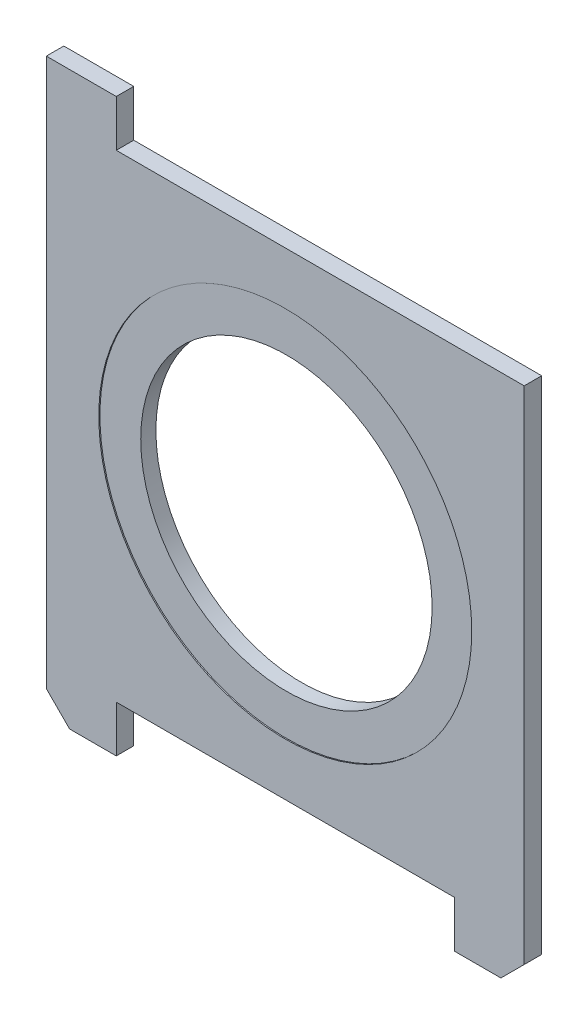
SolidWorks part; units mm, degrees
ref_plane "Plan de face" through (0, 0, 0) normal (0, 0, 1) x (1, 0, 0)
ref_plane "Plan de dessus" through (0, 0, 0) normal (0, 1, 0) x (1, 0, 0)
ref_plane "Plan de droite" through (0, 0, 0) normal (1, 0, 0) x (0, 0, -1)
sketch "Esquisse1" plane through (0, 0, 0) normal (0, 0, 1) x (1, 0, 0)
  line L1 (-20.5, -20.5) -> (20.5, -20.5)
  line L2 (-20.5, -20.5) -> (-20.5, 20.5)
  line L3 (-20.5, 20.5) -> (20.5, 20.5)
  line L4 (20.5, -20.5) -> (20.5, 20.5)
  line L5 (-20.5, -20.5) -> (20.5, 20.5) construction
  line L6 (-20.5, 20.5) -> (20.5, -20.5) construction
  point P0 (0, 0)
  dimension "D1" = 41
  dimension "D2" = 41
extrude "Boss.-Extru.1" add sketch "Esquisse1" along normal blind 1.5
sketch "Esquisse2" plane through (0, 0, 0) normal (0, 0, -1) x (-1, 0, 0)
  line L0 (0, -4.737) -> (0, -16.9551) construction
  line L1 (20.5, 20.5) -> (14.5, 20.5)
  line L2 (20.5, 20.5) -> (20.5, 24.5)
  line L3 (20.5, 24.5) -> (14.5, 24.5)
  line L4 (14.5, 20.5) -> (14.5, 24.5)
  line L5 (-20.5, -20.5) -> (-14.5, -20.5)
  line L6 (-20.5, -20.5) -> (-20.5, -24.5)
  line L7 (-20.5, -24.5) -> (-14.5, -24.5)
  line L8 (-14.5, -20.5) -> (-14.5, -24.5)
  line L9 (20.5, -24.5) -> (14.5, -24.5)
  line L10 (14.5, -20.5) -> (14.5, -24.5)
  line L11 (20.5, -20.5) -> (14.5, -20.5)
  line L12 (20.5, -20.5) -> (20.5, -24.5)
  dimension "D1" = 6
  dimension "D2" = 4
  dimension "D3" = 4
  dimension "D4" = 6
extrude "Boss.-Extru.2" add sketch "Esquisse2" against normal up to surface (1.5 mm away) up to face at (0, 0, 1.5)
sketch "Esquisse3" plane through (0, 0, 0) normal (0, 0, -1) x (-1, 0, 0)
  circle A0 centre (0, 0) radius 12.5
  dimension "D1" = 25
extrude "Enlèv. mat.-Extru.1" cut sketch "Esquisse3" against normal through all
sketch "Esquisse4" plane through (0, 0, 0) normal (0, 0, -1) x (-1, 0, 0)
  circle A0 centre (0, 0) radius 16
  dimension "D1" = 32
extrude "Enlèv. mat.-Extru.2" cut sketch "Esquisse4" against normal blind 0.1
sketch "Esquisse5" plane through (0, 0, 1.5) normal (0, 0, 1) x (1, 0, 0)
  circle A0 centre (0, 0) radius 16
  dimension "D1" = 32
extrude "Enlèv. mat.-Extru.3" cut sketch "Esquisse5" against normal blind 0.1
chamfer "Chanfrein1" distance 2 angle 45 1 edges at (-20.5, -24.5, 0.75)
chamfer "Chanfrein2" distance 2 angle 45 1 edges at (20.5, -24.5, 0.75)
